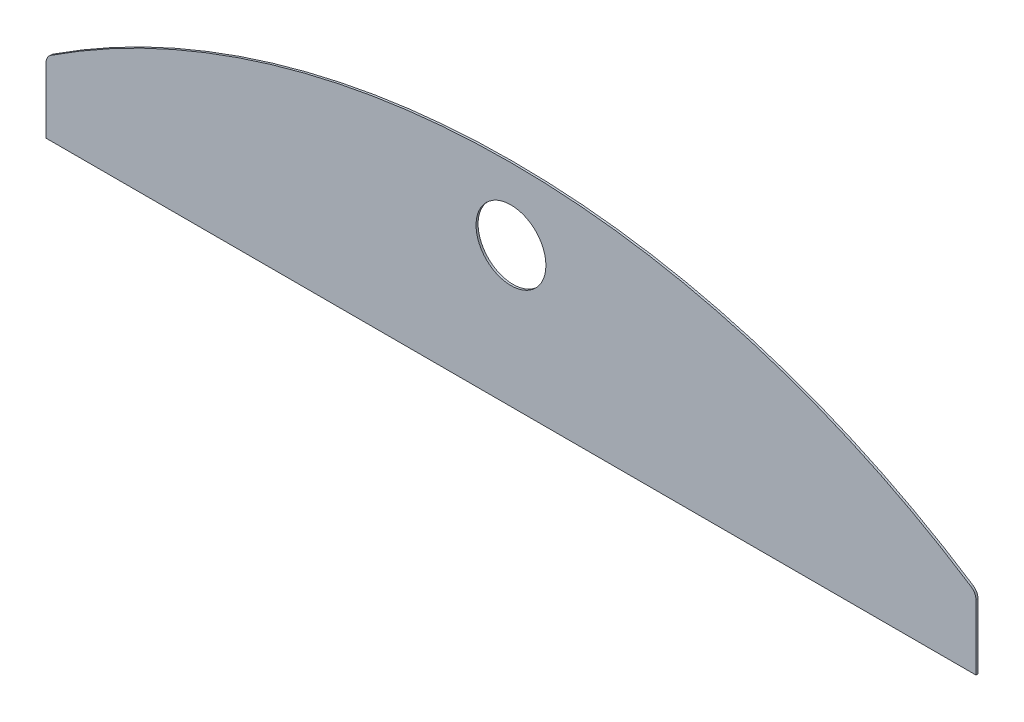
SolidWorks part; units mm, degrees
ref_plane "Front Plane" through (0, 0, 0) normal (0, 0, 1) x (1, 0, 0)
ref_plane "Top Plane" through (0, 0, 0) normal (0, 1, 0) x (1, 0, 0)
ref_plane "Right Plane" through (0, 0, 0) normal (1, 0, 0) x (0, 0, -1)
sketch "Sketch1" plane through (0, 0, 0) normal (0, 0, 1) x (1, 0, 0)
  line L1 (-338.05, 1029.9678) -> (-338.05, 1077.345) construction
  line L3 (-338.05, 1029.9678) -> (-338.05, 1077.345)
  line L4 (338.05, 1029.9678) -> (338.05, 1077.345) construction
  line L5 (338.05, 1029.9678) -> (338.05, 1077.345)
  line L6 (338.05, 1029.9678) -> (-338.05, 1029.9678)
  arc A0 (334.4968, 1083.9146) -> (-334.4968, 1083.9146) centre (0, 572.49) ccw construction
  arc A1 (334.4968, 1083.9146) -> (-334.4968, 1083.9146) centre (0, 572.49) ccw
  arc A5 (-334.4968, 1083.9146) -> (-338.05, 1077.345) centre (-330.2, 1077.345) ccw construction
  arc A6 (-334.4968, 1083.9146) -> (-338.05, 1077.345) centre (-330.2, 1077.345) ccw
  arc A7 (338.05, 1077.345) -> (334.4968, 1083.9146) centre (330.2, 1077.345) ccw construction
  arc A8 (338.05, 1077.345) -> (334.4968, 1083.9146) centre (330.2, 1077.345) ccw
extrude "Extrude1" add sketch "Sketch1" along normal blind 1.5
sketch "Sketch2" plane through (0, 0, 1.5) normal (0, 0, 1) x (1, 0, 0)
  line L0 (0, 1029.9678) -> (0, 1131.5678) construction
  line L1 (-338.05, 1029.9678) -> (338.05, 1029.9678) construction
  circle A0 centre (0, 1131.5678) radius 25.4
  dimension "D1" = 50.8
  dimension "D3" = 101.6
extrude "Cut-Extrude1" cut sketch "Sketch2" against normal through all
